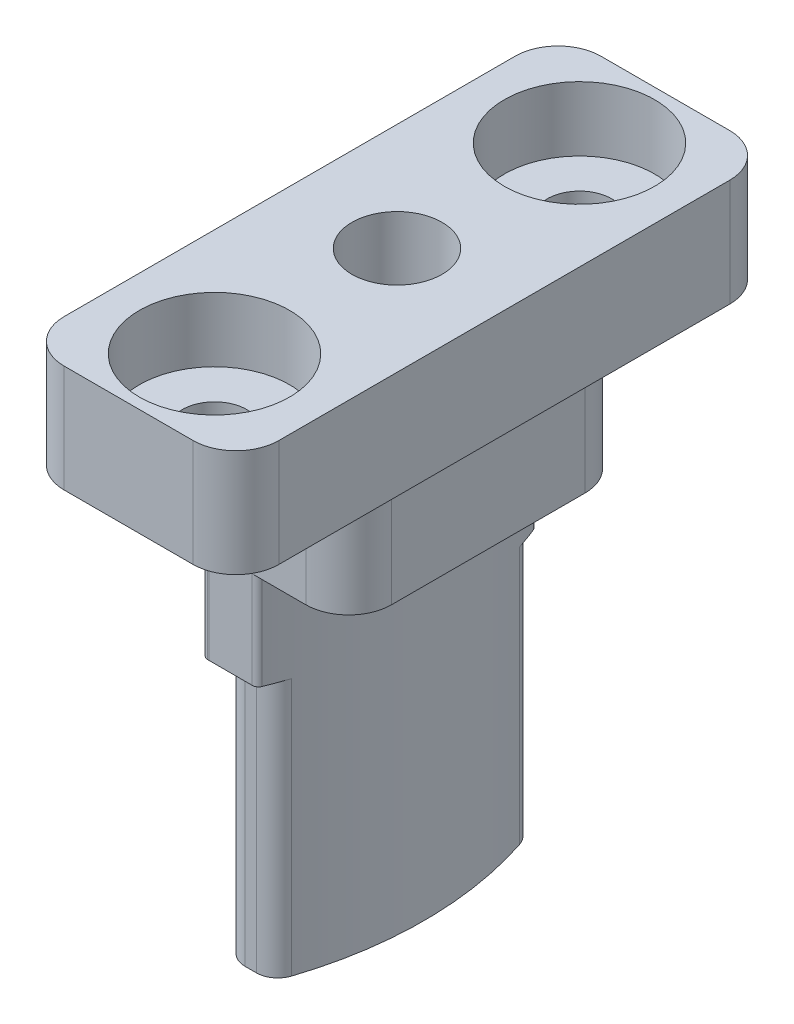
SolidWorks part; units mm, degrees
ref_plane "Front Plane" through (0, 0, 0) normal (0, 0, 1) x (1, 0, 0)
ref_plane "Top Plane" through (0, 0, 0) normal (0, 1, 0) x (1, 0, 0)
ref_plane "Right Plane" through (0, 0, 0) normal (1, 0, 0) x (0, 0, -1)
sketch "Sketch1" plane through (0, 0, 0) normal (0, 1, 0) x (1, 0, 0)
  line L1 (0, 0) -> (123.5, 0)
  line L2 (0, 0) -> (0, -81.5)
  line L3 (0, -81.5) -> (123.5, -81.5)
  line L4 (123.5, 0) -> (123.5, -81.5)
  dimension "D1" = 123.5
  dimension "D2" = 81.5
extrude "Boss-Extrude1" add sketch "Sketch1" along normal blind 8
chamfer "Chamfer1" distance 10 angle 45 2 edges at (123.5, 4, 81.5) (123.5, 4, 0)
sketch "Sketch2" plane through (0, 0, 0) normal (0, -1, 0) x (1, 0, 0)
  line L0 (0, 0) -> (0, 81.5) construction
  line L1 (-3.25, -3.25) -> (126.75, -3.25)
  line L2 (-3.25, -3.25) -> (-3.25, 84.75)
  line L3 (-3.25, 84.75) -> (126.75, 84.75)
  line L4 (126.75, -3.25) -> (126.75, 84.75)
  line L5 (113.5, 0) -> (0, 0) construction
  dimension "D1" = 88
  dimension "D2" = 130
  dimension "D3" = 3.25
  dimension "D4" = 3.25
extrude "Boss-Extrude2" add sketch "Sketch2" along normal blind 9
fillet "Fillet1" radius 2 10 edges at (113.5, 4, 0) (123.5, 4, 10) (123.5, 4, 71.5) (113.5, 4, 81.5) (126.75, -4.5, 84.75) (126.75, -4.5, -3.25) (-3.25, -4.5, -3.25) (0, 4, 0) (-3.25, -4.5, 84.75) (0, 4, 81.5)
sketch "Sketch3" plane through (0, -9, 0) normal (0, -1, 0) x (1, 0, 0)
  line L0 (-3.25, 82.75) -> (-3.25, -1.25) construction
  line L1 (-0.25, 81.75) -> (123.75, 81.75)
  line L2 (-0.25, 81.75) -> (-0.25, -0.25)
  line L3 (-0.25, -0.25) -> (123.75, -0.25)
  line L4 (123.75, 81.75) -> (123.75, -0.25)
  line L5 (-1.25, -3.25) -> (124.75, -3.25) construction
  dimension "D1" = 82
  dimension "D2" = 124
  dimension "D3" = 3
  dimension "D4" = 3
extrude "Cut-Extrude1" cut sketch "Sketch3" against normal blind 2
fillet "Fillet2" radius 2 4 edges at (123.75, -8, 81.75) (123.75, -8, -0.25) (-0.25, -8, -0.25) (-0.25, -8, 81.75)
sketch "Sketch4" plane through (0, 8, 0) normal (0, 1, 0) x (1, 0, 0)
  line L0 (-3.25, -82.75) -> (-3.25, 1.25) construction
  line L1 (112.6716, 0) -> (2, 0) construction
  line L2 (126.75, -40.75) -> (-3.25, -40.75) construction
  line L3 (126.75, 1.25) -> (126.75, -82.75) construction
  circle A0 centre (22.5, -20.85) radius 10
  circle A1 centre (61.5, -20.85) radius 10
  circle A2 centre (100.5, -20.85) radius 10
  circle A3 centre (100.5, -60.65) radius 10
  circle A4 centre (61.5, -60.65) radius 10
  circle A5 centre (22.5, -60.65) radius 10
  dimension "D1" = 25.75
  dimension "D2" = 39
  dimension "D3" = 39
  dimension "D4" = 20.85
  dimension "D5" = 20
extrude "Cut-Extrude2" cut sketch "Sketch4" against normal through all
sketch "Sketch5" plane through (0, -7, 0) normal (0, -1, 0) x (1, 0, 0)
  line L0 (126.75, 40.75) -> (-3.25, 40.75) construction
  line L1 (126.75, -1.25) -> (126.75, 82.75) construction
  line L2 (-3.25, 82.75) -> (-3.25, -1.25) construction
  circle A0 centre (22.5, 60.65) radius 14.5
  circle A1 centre (22.5, 60.65) radius 17
  circle A2 centre (61.5, 60.65) radius 14.5
  circle A3 centre (61.5, 60.65) radius 17
  circle A4 centre (100.5, 60.65) radius 14.5
  circle A5 centre (100.5, 60.65) radius 17
  circle A6 centre (100.5, 20.85) radius 17
  circle A7 centre (100.5, 20.85) radius 14.5
  circle A8 centre (61.5, 20.85) radius 17
  circle A9 centre (61.5, 20.85) radius 14.5
  circle A10 centre (22.5, 20.85) radius 17
  circle A11 centre (22.5, 20.85) radius 14.5
  dimension "D1" = 29
  dimension "D2" = 34
extrude "Boss-Extrude3" add sketch "Sketch5" along normal blind 16.5
sketch "Sketch6" plane through (0, -23.5, 0) normal (0, -1, 0) x (1, 0, 0)
  line L0 (100.5, 20.85) -> (142.0051, 20.85) construction
  line L1 (4.5, 26.85) -> (118.5, 26.85)
  line L2 (4.5, 26.85) -> (4.5, 14.85)
  line L3 (4.5, 14.85) -> (118.5, 14.85)
  line L4 (118.5, 26.85) -> (118.5, 14.85)
  line L5 (126.75, 40.75) -> (-3.25, 40.75) construction
  line L6 (-23.5, 39.1) -> (146.5, 39.1)
  line L7 (-23.5, 39.1) -> (-23.5, 2.6)
  line L8 (-23.5, 2.6) -> (146.5, 2.6)
  line L9 (146.5, 39.1) -> (146.5, 2.6)
  line L10 (-23.5, 39.1) -> (146.5, 2.6) construction
  line L11 (-23.5, 2.6) -> (146.5, 39.1) construction
  line L12 (126.75, -1.25) -> (126.75, 82.75) construction
  line L13 (-3.25, 82.75) -> (-3.25, -1.25) construction
  line L14 (-23.5, 78.9) -> (146.5, 42.4) construction
  line L15 (-23.5, 42.4) -> (146.5, 78.9) construction
  line L16 (100.5, 60.65) -> (142.0051, 60.65) construction
  line L17 (146.5, 42.4) -> (146.5, 78.9)
  line L18 (-23.5, 78.9) -> (146.5, 78.9)
  line L19 (-23.5, 42.4) -> (-23.5, 78.9)
  line L20 (-23.5, 42.4) -> (146.5, 42.4)
  line L21 (118.5, 54.65) -> (118.5, 66.65)
  line L22 (4.5, 66.65) -> (118.5, 66.65)
  line L23 (4.5, 54.65) -> (4.5, 66.65)
  line L24 (4.5, 54.65) -> (118.5, 54.65)
  circle A0 centre (22.5, 20.85) radius 10 construction
  point P11 (61.5, 20.85)
  point P31 (61.5, 60.65)
  dimension "D1" = 6
  dimension "D2" = 12
  dimension "D3" = 18
  dimension "D4" = 18
  dimension "D5" = 36.5
  dimension "D6" = 170
extrude "Cut-Extrude3" cut sketch "Sketch6" against normal blind 12
fillet "Fillet3" radius 1 48 edges at (6.594, -17.5, 66.65) (38.406, -17.5, 66.65) (35.7004, -17.5, 66.65) (9.2996, -17.5, 66.65) (9.2996, -17.5, 54.65) (35.7004, -17.5, 54.65) (6.594, -17.5, 54.65) (38.406, -17.5, 54.65) (74.7004, -17.5, 66.65) (48.2996, -17.5, 66.65) (45.594, -17.5, 66.65) (77.406, -17.5, 66.65) (48.2996, -17.5, 54.65) (74.7004, -17.5, 54.65) (45.594, -17.5, 54.65) (77.406, -17.5, 54.65) (113.7004, -17.5, 66.65) (87.2996, -17.5, 66.65) (84.594, -17.5, 66.65) (116.406, -17.5, 66.65) (87.2996, -17.5, 54.65) (113.7004, -17.5, 54.65) (84.594, -17.5, 54.65) (116.406, -17.5, 54.65) (113.7004, -17.5, 26.85) (87.2996, -17.5, 26.85) (116.406, -17.5, 26.85) (84.594, -17.5, 26.85) (116.406, -17.5, 14.85) (84.594, -17.5, 14.85) (87.2996, -17.5, 14.85) (113.7004, -17.5, 14.85) (48.2996, -17.5, 14.85) (74.7004, -17.5, 14.85) (77.406, -17.5, 14.85) (45.594, -17.5, 14.85) (77.406, -17.5, 26.85) (45.594, -17.5, 26.85) (74.7004, -17.5, 26.85) (48.2996, -17.5, 26.85) (38.406, -17.5, 26.85) (6.594, -17.5, 26.85) (35.7004, -17.5, 26.85) (9.2996, -17.5, 26.85) (38.406, -17.5, 14.85) (6.594, -17.5, 14.85) (9.2996, -17.5, 14.85) (35.7004, -17.5, 14.85)
sketch "Sketch7" plane through (0, -23.5, 0) normal (0, -1, 0) x (1, 0, 0)
  line L0 (22.5, 20.85) -> (9.8511, 20.85) construction
  line L1 (22.5, 20.85) -> (22.5, 13.7381) construction
  line L2 (22.5, 20.85) -> (61.5, 20.85) construction
  line L3 (42, 20.85) -> (42, 5.6594) construction
  line L4 (100.5, 20.85) -> (61.5, 20.85) construction
  line L5 (81, 20.85) -> (81, 5.6594) construction
  line L6 (126.75, 40.75) -> (-3.25, 40.75) construction
  line L7 (126.75, -1.25) -> (126.75, 82.75) construction
  line L8 (-3.25, 82.75) -> (-3.25, -1.25) construction
  circle A0 centre (6.75, 20.85) radius 0.85
  circle A1 centre (38.25, 20.85) radius 0.85
  circle A2 centre (45.75, 20.85) radius 0.85
  circle A3 centre (77.25, 20.85) radius 0.85
  circle A4 centre (84.75, 20.85) radius 0.85
  circle A5 centre (116.25, 20.85) radius 0.85
  circle A6 centre (116.25, 60.65) radius 0.85
  circle A7 centre (84.75, 60.65) radius 0.85
  circle A8 centre (77.25, 60.65) radius 0.85
  circle A9 centre (45.75, 60.65) radius 0.85
  circle A10 centre (38.25, 60.65) radius 0.85
  circle A11 centre (6.75, 60.65) radius 0.85
  dimension "D1" = 1.7
  dimension "D2" = 15.75
extrude "Cut-Extrude4" cut sketch "Sketch7" against normal blind 20.75
sketch "Sketch11" plane through (0, 0, 0) normal (0, 0, -1) x (-1, 0, 0)
  line L1 (-126.75, 10) -> (3.25, 10)
  line L2 (-126.75, 10) -> (-126.75, 0)
  line L3 (-126.75, 0) -> (3.25, 0)
  line L4 (3.25, 10) -> (3.25, 0)
  dimension "D1" = 10
extrude "Cut-Extrude8" cut sketch "Sketch11" against normal through all
sketch "Sketch13" plane through (0, 0, 0) normal (0, 1, 0) x (1, 0, 0)
  line L0 (77.25, -20.85) -> (80.5958, -20.85) construction
  line L1 (77.25, -60.65) -> (63.0285, -60.65) construction
  circle A0 centre (116.25, -60.65) radius 2.1
  circle A1 centre (85.5, -60.65) radius 2.1
  circle A2 centre (76.5, -60.65) radius 2.1
  circle A3 centre (116.25, -20.85) radius 2.1
  circle A4 centre (85.5, -20.85) radius 2.1
  circle A5 centre (76.5, -20.85) radius 2.1
  circle A6 centre (46.5, -20.85) radius 2.1
  circle A7 centre (37.5, -20.85) radius 2.1
  circle A8 centre (6.75, -20.85) radius 2.1
  circle A9 centre (6.75, -60.65) radius 2.1
  circle A10 centre (37.5, -60.65) radius 2.1
  circle A11 centre (46.5, -60.65) radius 2.1
  circle A12 centre (84.75, -60.65) radius 0.85 construction
  circle A13 centre (77.25, -60.65) radius 0.85 construction
  circle A14 centre (45.75, -60.65) radius 0.85 construction
  circle A15 centre (38.25, -60.65) radius 0.85 construction
  circle A16 centre (45.75, -20.85) radius 0.85 construction
  circle A17 centre (38.25, -20.85) radius 0.85 construction
  circle A18 centre (77.25, -20.85) radius 0.85 construction
  circle A19 centre (84.75, -20.85) radius 0.85 construction
  dimension "D1" = 4.2
  dimension "D3" = 0.75
  dimension "D2" = 0.75
  dimension "D4" = 0.75
  dimension "D5" = 0.75
  dimension "D6" = 0.75
  dimension "D7" = 0.75
  dimension "D8" = 0.75
  dimension "D9" = 0.75
extrude "Cut-Extrude9" cut sketch "Sketch13" against normal blind 6
sketch "Sketch15" plane through (0, 0, 0) normal (0, 1, 0) x (1, 0, 0)
  line L4 (126.75, -82.75) -> (126.75, 1.25)
  line L5 (124.75, 3.25) -> (-1.25, 3.25)
  line L6 (-3.25, 1.25) -> (-3.25, -82.75)
  line L7 (-1.25, -84.75) -> (124.75, -84.75)
  line L8 (126.75, -82.75) -> (126.75, 1.25)
  line L9 (124.75, 3.25) -> (-1.25, 3.25)
  line L10 (-3.25, 1.25) -> (-3.25, -82.75)
  line L11 (-1.25, -84.75) -> (124.75, -84.75)
  circle A0 centre (6.75, -60.65) radius 2.1 construction
  circle A1 centre (22.5, -60.65) radius 10 construction
  circle A2 centre (37.5, -60.65) radius 2.1 construction
  circle A3 centre (46.5, -60.65) radius 2.1 construction
  arc A4 (124.75, -84.75) -> (126.75, -82.75) centre (124.75, -82.75) ccw
  arc A5 (126.75, 1.25) -> (124.75, 3.25) centre (124.75, 1.25) ccw
  arc A6 (-1.25, 3.25) -> (-3.25, 1.25) centre (-1.25, 1.25) ccw
  arc A7 (-3.25, -82.75) -> (-1.25, -84.75) centre (-1.25, -82.75) ccw
  arc A8 (124.75, -84.75) -> (126.75, -82.75) centre (124.75, -82.75) ccw
  arc A9 (126.75, 1.25) -> (124.75, 3.25) centre (124.75, 1.25) ccw
  arc A10 (-1.25, 3.25) -> (-3.25, 1.25) centre (-1.25, 1.25) ccw
  arc A11 (-3.25, -82.75) -> (-1.25, -84.75) centre (-1.25, -82.75) ccw
  circle A12 centre (61.5, -60.65) radius 10 construction
  circle A13 centre (76.5, -60.65) radius 2.1 construction
  circle A14 centre (100.5, -60.65) radius 10 construction
  circle A15 centre (116.25, -60.65) radius 2.1 construction
  circle A16 centre (116.25, -20.85) radius 2.1 construction
  circle A17 centre (100.5, -20.85) radius 10 construction
  circle A18 centre (85.5, -20.85) radius 2.1 construction
  circle A19 centre (76.5, -20.85) radius 2.1 construction
  circle A20 centre (61.5, -20.85) radius 10 construction
  circle A21 centre (46.5, -20.85) radius 2.1 construction
  circle A22 centre (37.5, -20.85) radius 2.1 construction
  circle A23 centre (22.5, -20.85) radius 10 construction
  circle A24 centre (6.75, -60.65) radius 2.1
  circle A25 centre (22.5, -60.65) radius 10
  circle A26 centre (37.5, -60.65) radius 2.1
  circle A27 centre (46.5, -60.65) radius 2.1
  circle A28 centre (61.5, -60.65) radius 10
  circle A29 centre (76.5, -60.65) radius 2.1
  circle A30 centre (100.5, -60.65) radius 10
  circle A31 centre (116.25, -60.65) radius 2.1
  circle A32 centre (116.25, -20.85) radius 2.1
  circle A33 centre (100.5, -20.85) radius 10
  circle A34 centre (85.5, -20.85) radius 2.1
  circle A35 centre (76.5, -20.85) radius 2.1
  circle A36 centre (61.5, -20.85) radius 10
  circle A37 centre (46.5, -20.85) radius 2.1
  circle A38 centre (37.5, -20.85) radius 2.1
  circle A39 centre (22.5, -20.85) radius 10
  circle A40 centre (85.5, -60.65) radius 2.1 construction
  circle A41 centre (85.5, -60.65) radius 2.1
  circle A42 centre (6.75, -20.85) radius 2.1 construction
  circle A43 centre (6.75, -20.85) radius 2.1
  dimension "D1" = 0
extrude "Boss-Extrude4" add sketch "Sketch15" along normal blind 3
sketch "Sketch16" plane through (0, 3, 0) normal (0, 1, 0) x (1, 0, 0)
  line L0 (-1.25, -84.75) -> (124.75, -84.75) construction
  line L2 (-23.2035, 15.0774) -> (164.8737, 15.0774)
  line L3 (-23.2035, 15.0774) -> (-23.2035, -102.024)
  line L4 (-23.2035, -102.024) -> (164.8737, -102.024)
  line L5 (164.8737, 15.0774) -> (164.8737, -102.024)
  line L8 (111.25, -48.15) -> (121.25, -48.15)
  line L9 (111.25, -48.15) -> (111.25, -73.15)
  line L10 (111.25, -73.15) -> (121.25, -73.15)
  line L11 (121.25, -48.15) -> (121.25, -73.15)
  line L12 (111.25, -48.15) -> (121.25, -73.15) construction
  line L13 (111.25, -73.15) -> (121.25, -48.15) construction
  point P9 (116.25, -60.65)
  dimension "D1" = 11.6
  dimension "D3" = 10
extrude "Cut-Extrude10" cut sketch "Sketch16" against normal through all
sketch "Sketch17" plane through (0, 3, 0) normal (0, 1, 0) x (1, 0, 0)
  line L1 (112, -67.15) -> (120.5, -67.15)
  line L2 (112, -67.15) -> (112, -54.15)
  line L3 (112, -54.15) -> (120.5, -54.15)
  line L4 (120.5, -67.15) -> (120.5, -54.15)
  line L5 (112, -67.15) -> (120.5, -54.15) construction
  line L6 (112, -54.15) -> (120.5, -67.15) construction
  line L7 (111.25, -73.15) -> (121.25, -73.15)
  line L8 (111.25, -73.15) -> (111.25, -48.15)
  line L9 (111.25, -48.15) -> (121.25, -48.15)
  line L10 (121.25, -73.15) -> (121.25, -48.15)
  point P0 (116.25, -60.65)
  dimension "D1" = 13
  dimension "D2" = 8.5
extrude "Cut-Extrude11" cut sketch "Sketch17" against normal through all from offset 5 offset against normal yes
fillet "Fillet4" radius 2 8 edges at (120.5, -4.5, 54.15) (121.25, 0.5, 48.15) (120.5, -4.5, 67.15) (112, -4.5, 54.15) (112, -4.5, 67.15) (121.25, 0.5, 73.15) (111.25, 0.5, 73.15) (111.25, 0.5, 48.15)
sketch "Sketch18" plane through (0, 3, 0) normal (0, 1, 0) x (1, 0, 0)
  line L0 (119.25, -48.15) -> (113.25, -48.15) construction
  line L1 (116.25, -60.65) -> (130.1274, -60.65) construction
  circle A0 centre (116.25, -52.15) radius 1.5
  circle A1 centre (116.25, -69.15) radius 1.5
  point P5 (116.25, -48.15)
  dimension "D1" = 3
  dimension "D2" = 4
extrude "Cut-Extrude12" cut sketch "Sketch18" against normal through all
sketch "Sketch19" plane through (0, 3, 0) normal (0, 1, 0) x (1, 0, 0)
  circle A0 centre (116.25, -52.15) radius 3.5
  circle A1 centre (116.25, -69.15) radius 3.5
  dimension "D1" = 7
extrude "Cut-Extrude13" cut sketch "Sketch19" against normal blind 3
fillet "Fillet5" radius 0.3 4 edges at (116.2083, -9.25, 54.15) (113.4939, -9.25, 54.2151) (116.2083, -9.25, 67.15) (113.4939, -9.25, 67.0849)
